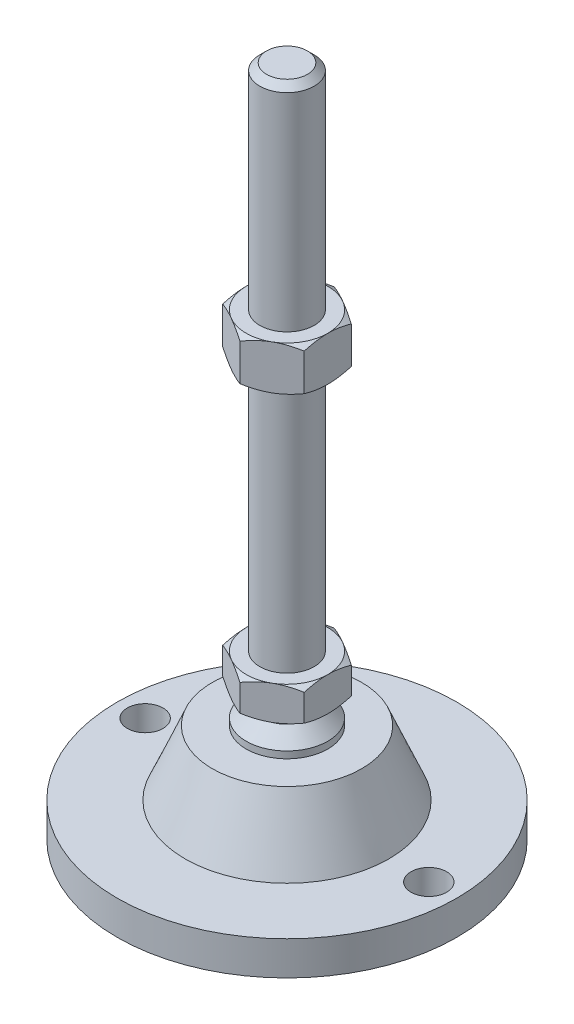
SolidWorks part; units mm, degrees
ref_plane "Спереди" through (0, 0, 0) normal (0, 0, 1) x (1, 0, 0)
ref_plane "Сверху" through (0, 0, 0) normal (0, 1, 0) x (1, 0, 0)
ref_plane "Справа" through (0, 0, 0) normal (1, 0, 0) x (0, 0, -1)
sketch "Эскиз1" plane through (0, 0, 0) normal (0, 0, 1) x (1, 0, 0)
  line L0 (0, 0) -> (-50, 0)
  line L3 (-50, 0) -> (-50, 10)
  line L12 (-8, 48) -> (-8, 196)
  line L13 (-8, 196) -> (-6, 198)
  line L14 (-6, 198) -> (0, 198)
  line L15 (0, 198) -> (0, 0) construction
  line L16 (-50, 10) -> (-30, 10)
  line L17 (0, 0) -> (0, 198)
  line L18 (0, 0) -> (0, -7.9595) construction
  line L19 (-8, 48) -> (-8, 38)
  line L21 (-12, 29) -> (-22, 29)
  line L22 (-30, 10) -> (-22, 29)
  line L23 (-12, 29) -> (-12, 31)
  line L24 (-12, 31) -> (-8, 35)
  line L25 (-8, 35) -> (-8, 38)
  line L26 (-8, 48) -> (0, 48) construction
  point P8 (-8, 122)
revolve "Повернуть1" add sketch "Эскиз1" angle 360 about L17
ref_plane "Плоскость2" through (0, 38, 0) normal (0, 1, 0) x (1, 0, 0)
sketch "Эскиз2" plane through (0, 38, 0) normal (0, 1, 0) x (1, 0, 0)
  line L1 (0, 13.8564) -> (-12, 6.9282)
  line L2 (-12, 6.9282) -> (-12, -6.9282)
  line L3 (-12, -6.9282) -> (0, -13.8564)
  line L4 (0, -13.8564) -> (12, -6.9282)
  line L5 (12, -6.9282) -> (12, 6.9282)
  line L6 (12, 6.9282) -> (0, 13.8564)
  circle A0 centre (0, 0) radius 12 construction
  dimension "D1" = 24
extrude "Бобышка-Вытянуть1" add sketch "Эскиз2" along normal up to vertex (10 mm away) up to point (-8, 48, 0)
ref_plane "Плоскость1" through (0, 122, 0) normal (0, 1, 0) x (1, 0, 0)
sketch "Эскиз3" plane through (0, 122, 0) normal (0, 1, 0) x (1, 0, 0)
  line L6 (12, 6.9282) -> (0, 13.8564)
  line L7 (0, 13.8564) -> (-12, 6.9282)
  line L8 (-12, 6.9282) -> (-12, -6.9282)
  line L9 (-12, -6.9282) -> (0, -13.8564)
  line L10 (0, -13.8564) -> (12, -6.9282)
  line L11 (12, -6.9282) -> (12, 6.9282)
  line L12 (12, 6.9282) -> (0, 13.8564)
  line L13 (0, 13.8564) -> (-12, 6.9282)
  line L14 (-12, 6.9282) -> (-12, -6.9282)
  line L15 (-12, -6.9282) -> (0, -13.8564)
  line L16 (0, -13.8564) -> (12, -6.9282)
  line L17 (12, -6.9282) -> (12, 6.9282)
  dimension "D1" = 0
extrude "Бобышка-Вытянуть2" add sketch "Эскиз3" along normal blind 13
sketch "Эскиз4" plane through (0, 0, 0) normal (0, 0, 1) x (1, 0, 0)
  line L0 (-12, 135) -> (-23.2583, 128.5)
  line L1 (-23.2583, 128.5) -> (-23.2583, 135)
  line L2 (-23.2583, 135) -> (-12, 135)
  line L3 (-23.2583, 128.5) -> (-12, 122)
  line L4 (50, 122) -> (-50, 122) construction
  line L5 (-12, 122) -> (-23.2583, 122)
  line L6 (-23.2583, 122) -> (-23.2583, 128.5)
  line L7 (-12, 135) -> (-12, 122) construction
  line L8 (-12, 48) -> (-20.6603, 48)
  line L9 (-20.6603, 48) -> (-20.6603, 43)
  line L10 (-20.6603, 43) -> (-12, 48)
  line L11 (-12, 38) -> (-20.6603, 43)
  line L12 (-20.6603, 43) -> (-20.6603, 38)
  line L13 (-20.6603, 38) -> (-12, 38)
  line L14 (0, 198) -> (0, 96.3793) construction
  line L15 (50, 38) -> (-50, 38) construction
  dimension "D1" = 30
  dimension "D2" = 30
revolve "Вырез-Повернуть2" cut sketch "Эскиз4" angle 360 about L14
sketch "Эскиз5" plane through (0, 10, 0) normal (0, 1, 0) x (1, 0, 0)
  line L0 (41.75, 0) -> (-41.75, 0) construction
  circle A0 centre (-41.75, 0) radius 5.25
  circle A1 centre (41.75, 0) radius 5.25
  circle A2 centre (0, 0) radius 50 construction
  dimension "D1" = 10.5
  dimension "D2" = 3
extrude "Вырез-Вытянуть1" cut sketch "Эскиз5" against normal through all
equation "\"D13@Эскиз1\"=\"D12@Эскиз1\"/2"
